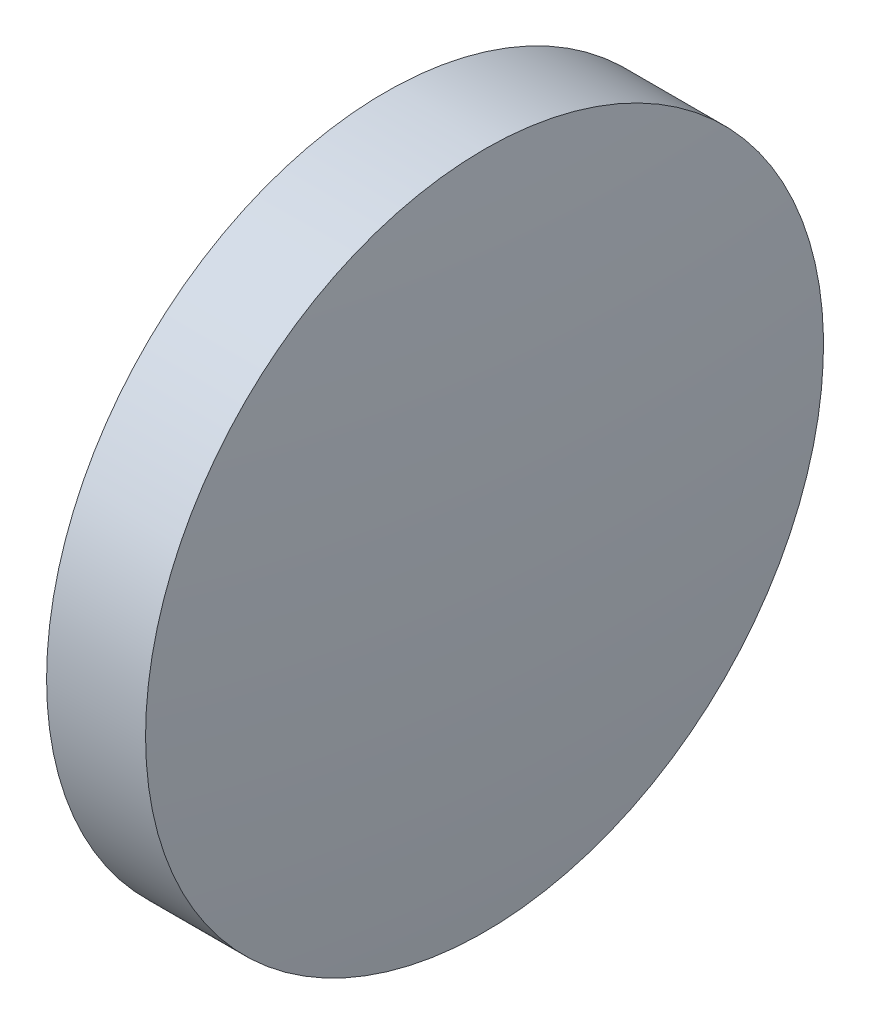
SolidWorks part; units mm, degrees
ref_plane "前视基准面" through (0, 0, 0) normal (0, 0, 1) x (1, 0, 0)
ref_plane "上视基准面" through (0, 0, 0) normal (0, 1, 0) x (1, 0, 0)
ref_plane "右视基准面" through (0, 0, 0) normal (1, 0, 0) x (0, 0, -1)
sketch "草图1" plane through (0, 0, 0) normal (0, 0, 1) x (1, 0, 0)
  line L0 (861.0148, 272.0668) -> (866.3931, 272.0668) construction
  line L1 (862.2463, 272.0668) -> (862.2463, 277.0668)
  line L2 (862.2463, 277.0668) -> (863.7063, 277.0668)
  line L3 (862.2463, 272.0668) -> (863.9463, 272.0668)
  arc A0 (863.9463, 272.0668) -> (863.7063, 277.0668) centre (811.743, 272.0668) ccw
revolve "旋转1" add sketch "草图1" angle 360 about L0
